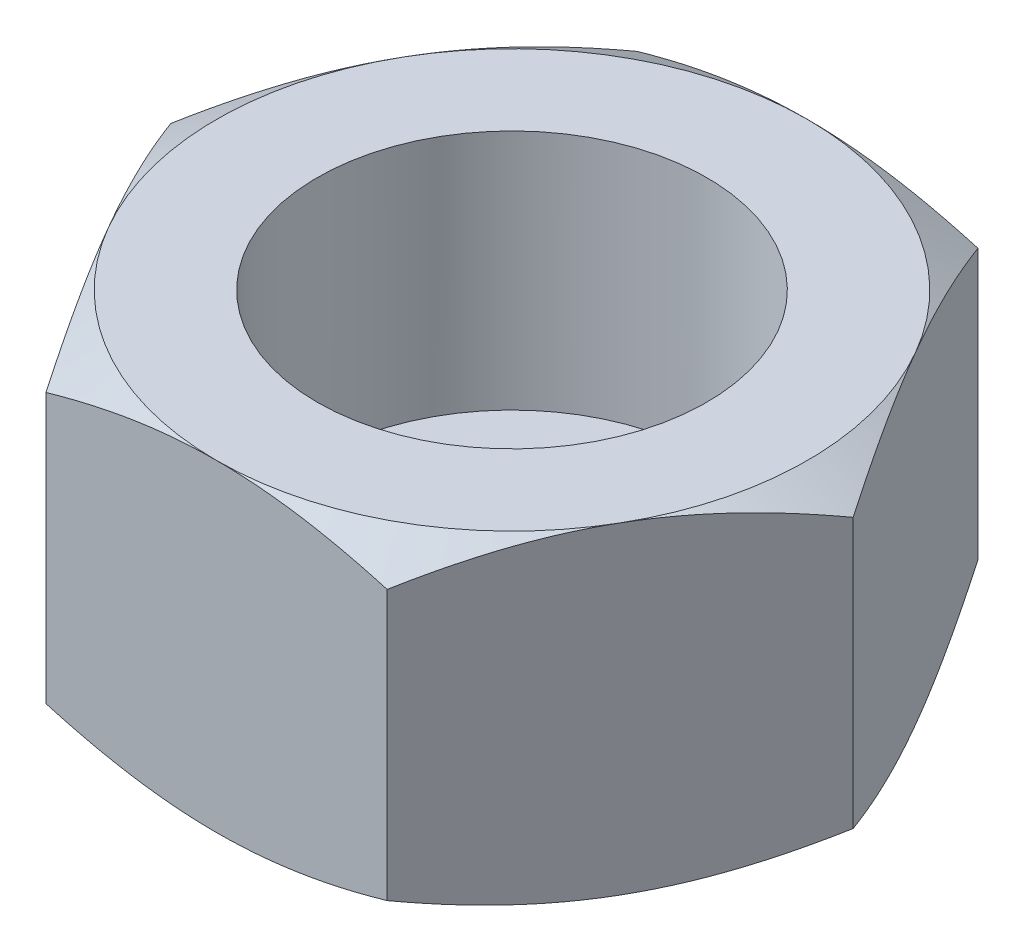
SolidWorks part; units mm, degrees
ref_plane "Ebene vorne" through (0, 0, 0) normal (0, 0, 1) x (1, 0, 0)
ref_plane "Ebene oben" through (0, 0, 0) normal (0, 1, 0) x (1, 0, 0)
ref_plane "Ebene rechts" through (0, 0, 0) normal (1, 0, 0) x (0, 0, -1)
sketch "Skizze1" plane through (0, 0, 0) normal (0, 1, 0) x (1, 0, 0)
  line L1 (12.7017, 0) -> (6.3509, 11)
  line L2 (6.3509, 11) -> (-6.3509, 11)
  line L3 (-6.3509, 11) -> (-12.7017, 0)
  line L4 (-12.7017, 0) -> (-6.3509, -11)
  line L5 (-6.3509, -11) -> (6.3509, -11)
  line L6 (6.3509, -11) -> (12.7017, 0)
  circle A0 centre (0, 0) radius 11 construction
  dimension "D1" = 22
extrude "Aufsatz-Linear austragen1" add sketch "Skizze1" along normal blind 12
sketch "Skizze2" plane through (0, 0, 0) normal (0, -1, 0) x (1, 0, 0)
  circle A0 centre (0, 0) radius 5
  dimension "D1" = 10
extrude "Schnitt-Linear austragen1" cut sketch "Skizze2" against normal blind 3
hole_wizard "M16x1.5 Gewindebohrung1" positions "Skizze3" profile "Skizze4" tap size "M16x1.5" standard "ISO" end condition up to next
sketch "Skizze3" plane through (0, 12, 0) normal (0, 1, 0) x (1, 0, 0)
  point P0 (0, 0)
sketch "Skizze4" plane through (0, 12, 0) normal (1, 0, 0) x (0, 0, 1)
  line L0 (0, 0) -> (0, 9)
  line L1 (0, 9) -> (7.25, 9)
  line L2 (7.25, 9) -> (7.25, 0)
  line L5 (7.25, 0) -> (0, 0)
  line L11 (0, -6.35) -> (0, 107.95) construction
  dimension "Bohrerdurchmesser" = 14.5
  dimension "Bohrungstiefe" = 9
cosmetic thread "Bohrungsgewinde1" parameters "D2"=16
sketch "Skizze5" plane through (0, 0, 0) normal (0, 0, 1) x (1, 0, 0)
  line L0 (0, 0) -> (0, 6.6646) construction
  line L1 (-12.7017, 12) -> (-11, 12)
  line L2 (-12.7017, 12) -> (-6.3509, 12) construction
  line L3 (-11, 12) -> (-12.7017, 11.0175)
  line L4 (-12.7017, 12) -> (-12.7017, 0) construction
  line L5 (-12.7017, 11.0175) -> (-12.7017, 12)
  line L6 (-12.7017, 0) -> (-11, 0)
  line L7 (-12.7017, 0) -> (-6.3509, 0) construction
  line L8 (-11, 0) -> (-12.7017, 0.9825)
  line L9 (-12.7017, 0.9825) -> (-12.7017, 0)
  dimension "D1" = 30
  dimension "D2" = 22
  dimension "D3" = 30
revolve "Schnitt-Rotation1" cut sketch "Skizze5" angle 360 about L0
